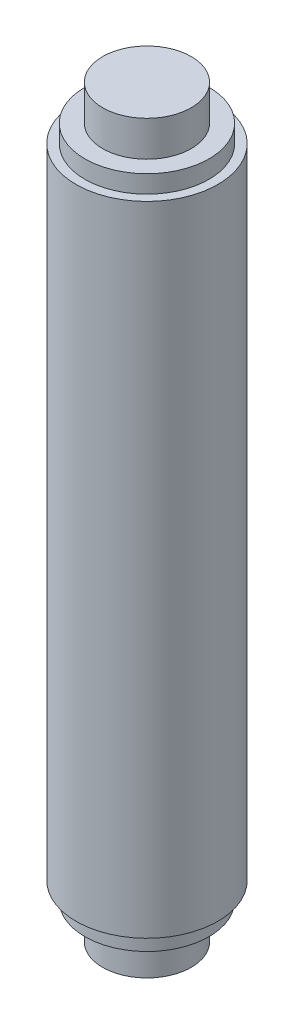
SolidWorks part; units mm, degrees
ref_plane "Front Plane" through (0, 0, 0) normal (0, 0, 1) x (1, 0, 0)
ref_plane "Top Plane" through (0, 0, 0) normal (0, 1, 0) x (1, 0, 0)
ref_plane "Right Plane" through (0, 0, 0) normal (1, 0, 0) x (0, 0, -1)
sketch "Sketch1" plane through (0, 0, 0) normal (0, 0, 1) x (1, 0, 0)
  line L0 (0, 21) -> (0, 0)
  line L1 (0, 21) -> (2.5, 21)
  line L2 (2.5, 21) -> (2.5, 19)
  line L3 (2.5, 19) -> (3.5, 19)
  line L4 (3.5, 19) -> (3.5, 18)
  line L5 (3.5, 18) -> (4, 18)
  line L7 (0, 0) -> (4, 0)
  line L10 (4, 18) -> (4, 0)
  circle A0 centre (19, 0) radius 15 construction
  point P2 (19, 0)
  dimension "D1" = 2.5
  dimension "D10" = 30
  dimension "D2" = 21
  dimension "D4" = 4
  dimension "D6" = 1
  dimension "D7" = 2
  dimension "D8" = 15
  dimension "D9" = 1
revolve "Revolve1" add sketch "Sketch1" angle 360 about L0
mirror "Mirror1" about plane through (0, 0, 0) normal (0, 1, 0) of "Revolve1"
